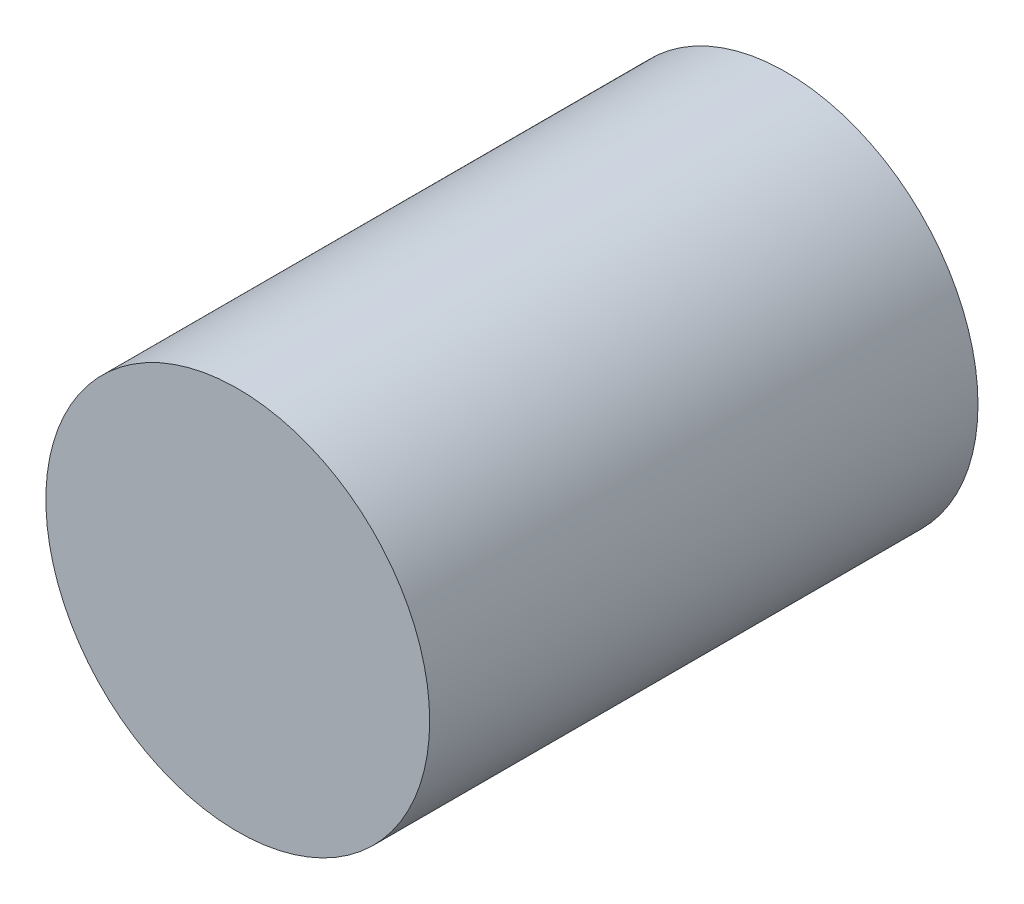
SolidWorks part; units mm, degrees
ref_plane "Front Plane" through (0, 0, 0) normal (0, 0, 1) x (1, 0, 0)
ref_plane "Top Plane" through (0, 0, 0) normal (0, 1, 0) x (1, 0, 0)
ref_plane "Right Plane" through (0, 0, 0) normal (1, 0, 0) x (0, 0, -1)
sketch "Sketch1" plane through (0, 0, 0) normal (0, 0, 1) x (1, 0, 0)
  circle A0 centre (0, 0) radius 3.5
extrude "Boss-Extrude1" add sketch "Sketch1" along normal blind 10
